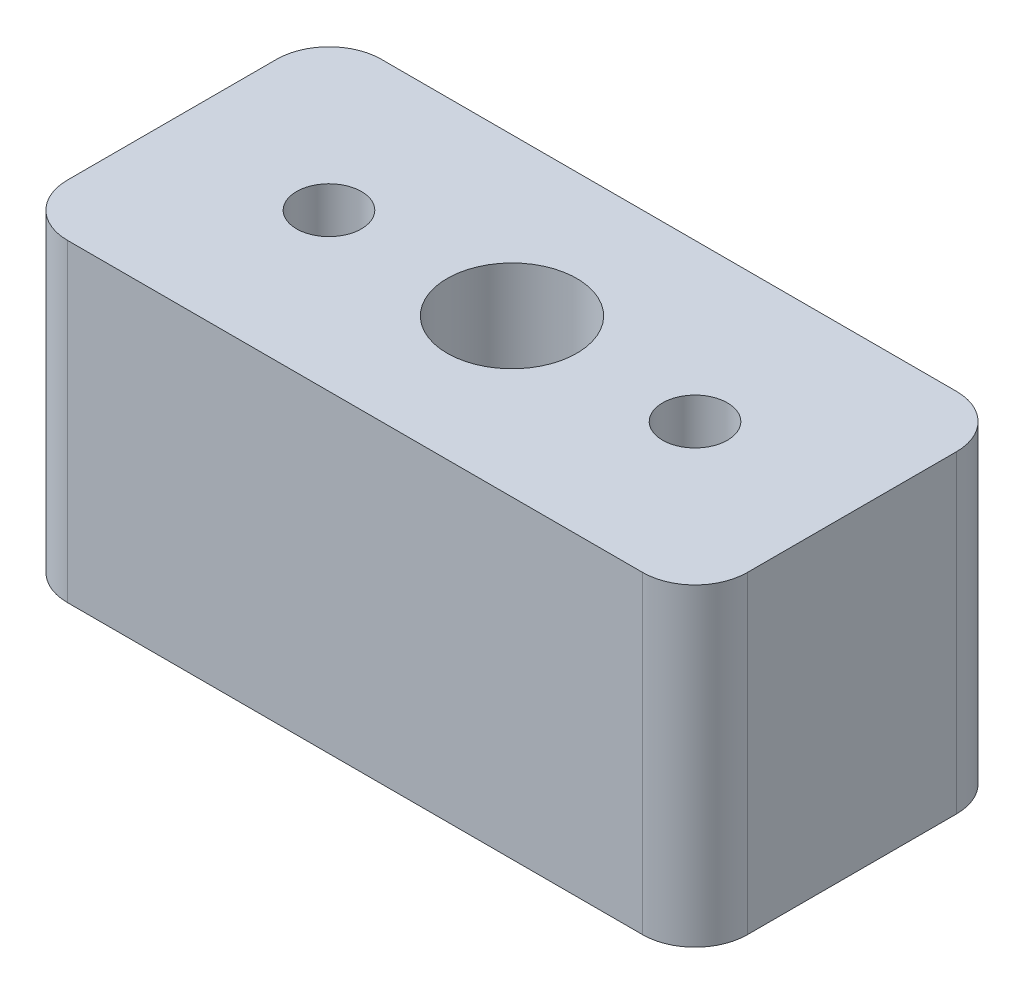
SolidWorks part; units mm, degrees
ref_plane "Front Plane" through (0, 0, 0) normal (0, 0, 1) x (1, 0, 0)
ref_plane "Top Plane" through (0, 0, 0) normal (0, 1, 0) x (1, 0, 0)
ref_plane "Right Plane" through (0, 0, 0) normal (1, 0, 0) x (0, 0, -1)
sketch "Sketch1" plane through (0, 0, 0) normal (0, 1, 0) x (1, 0, 0)
  line L0 (-3.25, -1.5) -> (3.25, -1.5)
  line L1 (-3.25, -1.5) -> (-3.25, 1.5)
  line L2 (3.25, -1.5) -> (3.25, 1.5)
  line L3 (-3.25, 1.5) -> (3.25, 1.5)
  line L6 (-3.25, 0) -> (3.25, 0) construction
  circle A0 centre (-1.75, 0) radius 0.31
  circle A1 centre (0, 0) radius 0.62
  circle A2 centre (1.75, 0) radius 0.31
  dimension "D5" = 0.62
  dimension "D9" = 1.24
  dimension "D10" = 0.62
  dimension "D2" = 3
  dimension "D3" = 1.75
  dimension "D4" = 1.75
  dimension "D6" = 1.5
  dimension "D7" = 3
  dimension "D11" = 1.5
extrude "Boss-Extrude1" add sketch "Sketch1" along normal blind 3
fillet "Fillet1" radius 0.5 4 edges at (3.25, 1.5, 1.5) (3.25, 1.5, -1.5) (-3.25, 1.5, -1.5) (-3.25, 1.5, 1.5)
